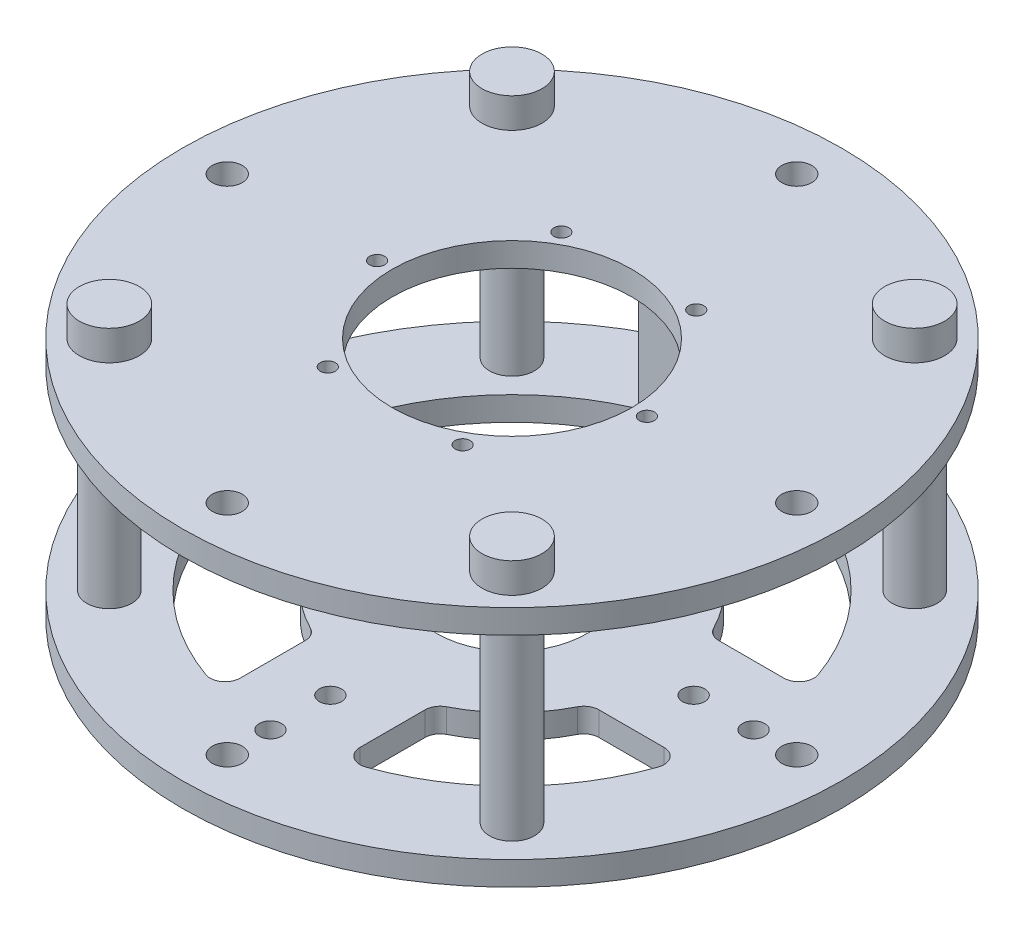
SolidWorks part; units mm, degrees
ref_plane "Front Plane" through (0, 0, 0) normal (0, 0, 1) x (1, 0, 0)
ref_plane "Top Plane" through (0, 0, 0) normal (0, 1, 0) x (1, 0, 0)
ref_plane "Right Plane" through (0, 0, 0) normal (1, 0, 0) x (0, 0, -1)
sketch "Sketch1" plane through (0, 0, 0) normal (0, 1, 0) x (1, 0, 0)
  line L0 (-25.4, 89.8026) -> (-25.4, 62.217)
  line L1 (25.4, 89.8026) -> (25.4, 62.217)
  line L2 (-25.4, 76.0098) -> (25.4, 76.0098) construction
  line L3 (0, 76.0098) -> (0, 0) construction
  line L4 (89.8026, 25.4) -> (62.217, 25.4)
  line L5 (89.8026, -25.4) -> (62.217, -25.4)
  line L6 (76.0098, 25.4) -> (76.0098, -25.4) construction
  line L7 (76.0098, 0) -> (0, 0) construction
  line L8 (25.4, -89.8026) -> (25.4, -62.217)
  line L9 (-25.4, -89.8026) -> (-25.4, -62.217)
  line L10 (25.4, -76.0098) -> (-25.4, -76.0098) construction
  line L11 (0, -76.0098) -> (0, 0) construction
  line L12 (-89.8026, -25.4) -> (-62.217, -25.4)
  line L13 (-89.8026, 25.4) -> (-62.217, 25.4)
  line L14 (-76.0098, -25.4) -> (-76.0098, 25.4) construction
  line L15 (-76.0098, 0) -> (0, 0) construction
  line L16 (0, 139.7) -> (0, 120.65) construction
  line L17 (0, 120.65) -> (0, 102.362) construction
  line L18 (0, 102.362) -> (0, 76.962) construction
  line L19 (98.7828, 98.7828) -> (85.3124, 85.3124) construction
  line L20 (139.7, 0) -> (120.65, 0) construction
  line L21 (98.7828, -98.7828) -> (85.3124, -85.3124) construction
  line L22 (0, -139.7) -> (0, -120.65) construction
  line L23 (-98.7828, -98.7828) -> (-85.3124, -85.3124) construction
  line L24 (-139.7, 0) -> (-120.65, 0) construction
  line L25 (-98.7828, 98.7828) -> (-85.3124, 85.3124) construction
  line L26 (139.7, 0) -> (120.65, 0) construction
  line L27 (120.65, 0) -> (102.362, 0) construction
  line L28 (102.362, 0) -> (76.962, 0) construction
  line L29 (0, -139.7) -> (0, -120.65) construction
  line L30 (0, -120.65) -> (0, -102.362) construction
  line L31 (0, -102.362) -> (0, -76.962) construction
  line L32 (-139.7, 0) -> (-120.65, 0) construction
  line L33 (-120.65, 0) -> (-102.362, 0) construction
  line L34 (-102.362, 0) -> (-76.962, 0) construction
  circle A0 centre (0, 0) radius 139.7
  arc A1 (-56.5609, -28.8636) -> (-28.8636, -56.5609) centre (0, 0) ccw
  arc A2 (-95.7894, -33.8667) -> (-33.8667, -95.7894) centre (0, 0) ccw
  circle A3 centre (0, 0) radius 31.75
  arc A4 (28.8636, -56.5609) -> (56.5609, -28.8636) centre (0, 0) ccw
  arc A5 (33.8667, -95.7894) -> (95.7894, -33.8667) centre (0, 0) ccw
  arc A6 (95.7894, 33.8667) -> (33.8667, 95.7894) centre (0, 0) ccw
  arc A7 (-33.8667, 95.7894) -> (-95.7894, 33.8667) centre (0, 0) ccw
  arc A8 (-28.8636, 56.5609) -> (-56.5609, 28.8636) centre (0, 0) ccw
  arc A9 (56.5609, 28.8636) -> (28.8636, 56.5609) centre (0, 0) ccw
  circle A10 centre (0, 120.65) radius 6.35
  circle A11 centre (0, 102.362) radius 4.699
  circle A12 centre (0, 76.962) radius 4.699
  circle A13 centre (85.3124, 85.3124) radius 6.35
  circle A14 centre (120.65, 0) radius 6.35
  circle A15 centre (85.3124, -85.3124) radius 6.35
  circle A16 centre (0, -120.65) radius 6.35
  circle A17 centre (-85.3124, -85.3124) radius 6.35
  circle A18 centre (-120.65, 0) radius 6.35
  circle A19 centre (-85.3124, 85.3124) radius 6.35
  circle A20 centre (120.65, 0) radius 6.35
  circle A21 centre (102.362, 0) radius 4.699
  circle A22 centre (76.962, 0) radius 4.699
  circle A23 centre (0, -120.65) radius 6.35
  circle A24 centre (0, -102.362) radius 4.699
  circle A25 centre (0, -76.962) radius 4.699
  circle A26 centre (-120.65, 0) radius 6.35
  circle A27 centre (-102.362, 0) radius 4.699
  circle A28 centre (-76.962, 0) radius 4.699
  arc A29 (-89.8026, 25.4) -> (-95.7894, 33.8667) centre (-89.8026, 31.75) cw
  arc A30 (-62.217, 25.4) -> (-56.5609, 28.8636) centre (-62.217, 31.75) ccw
  arc A31 (-25.4, 62.217) -> (-28.8636, 56.5609) centre (-31.75, 62.217) cw
  arc A32 (-25.4, 89.8026) -> (-33.8667, 95.7894) centre (-31.75, 89.8026) ccw
  arc A33 (25.4, 62.217) -> (28.8636, 56.5609) centre (31.75, 62.217) ccw
  arc A34 (25.4, 89.8026) -> (33.8667, 95.7894) centre (31.75, 89.8026) cw
  arc A35 (89.8026, 25.4) -> (95.7894, 33.8667) centre (89.8026, 31.75) ccw
  arc A36 (62.217, 25.4) -> (56.5609, 28.8636) centre (62.217, 31.75) cw
  arc A37 (89.8026, -25.4) -> (95.7894, -33.8667) centre (89.8026, -31.75) cw
  arc A38 (62.217, -25.4) -> (56.5609, -28.8636) centre (62.217, -31.75) ccw
  arc A39 (25.4, -62.217) -> (28.8636, -56.5609) centre (31.75, -62.217) cw
  arc A40 (25.4, -89.8026) -> (33.8667, -95.7894) centre (31.75, -89.8026) ccw
  arc A41 (-25.4, -89.8026) -> (-33.8667, -95.7894) centre (-31.75, -89.8026) cw
  arc A42 (-25.4, -62.217) -> (-28.8636, -56.5609) centre (-31.75, -62.217) ccw
  arc A43 (-62.217, -25.4) -> (-56.5609, -28.8636) centre (-62.217, -31.75) cw
  arc A44 (-89.8026, -25.4) -> (-95.7894, -33.8667) centre (-89.8026, -31.75) ccw
  point P37 (0, 0)
  point P63 (0, 0)
  point P86 (0, 0)
  point P90 (-25.4, 58.1987)
  point P93 (-25.4, 98.3738)
  point P96 (25.4, 58.1987)
  point P99 (25.4, 98.3738)
  dimension "D1" = 279.4
  dimension "D2" = 203.2
  dimension "D3" = 127
  dimension "D4" = 63.5
  dimension "D10" = 12.7
  dimension "D11" = 9.398
  dimension "D12" = 9.398
  dimension "D15" = 6.35
  dimension "D5" = 50.8
  dimension "D7" = 19.05
  dimension "D8" = 18.288
  dimension "D9" = 25.4
  dimension "D6" = 4
  dimension "D13" = 8
  dimension "D14" = 4
extrude "Boss-Extrude1" add sketch "Sketch1" along normal blind 10.16 contours A0 A44 L12 A43 A1 A42 L9 A41 A2 A40 L8 A39 A4 A38 L5 A37 A5 A32 L0 A31 A8 A30 L13 A29 A7 A28 A27 A25 A24 A22 A21 A19 A18 A17 A16 A15
sketch "Sketch2" plane through (0, 10.16, 0) normal (0, 1, 0) x (1, 0, 0)
  circle A0 centre (-85.3124, 85.3124) radius 9.525
  circle A1 centre (85.3124, 85.3124) radius 9.525
  circle A2 centre (85.3124, -85.3124) radius 9.525
  circle A3 centre (-85.3124, -85.3124) radius 9.525
  point P12 (0, 0)
  dimension "D1" = 19.05
  dimension "D2" = 4
extrude "Boss-Extrude2" add sketch "Sketch2" along normal blind 82.296
sketch "Sketch3" plane through (0, 92.456, 0) normal (0, 1, 0) x (1, 0, 0)
  circle A0 centre (0, 0) radius 139.7
  circle A1 centre (0, 0) radius 139.7 construction
  circle A2 centre (0, 0) radius 50.8
  circle A3 centre (0, 120.65) radius 6.35
  circle A4 centre (85.3124, 85.3124) radius 6.35
  circle A5 centre (120.65, 0) radius 6.35
  circle A6 centre (85.3124, -85.3124) radius 6.35
  circle A7 centre (0, -120.65) radius 6.35
  circle A8 centre (-85.3124, -85.3124) radius 6.35
  circle A9 centre (-120.65, 0) radius 6.35
  circle A10 centre (-85.3124, 85.3124) radius 6.35
  circle A11 centre (-57.15, 0) radius 3.175
  circle A12 centre (-28.575, 49.4934) radius 3.175
  circle A13 centre (28.575, 49.4934) radius 3.175
  circle A14 centre (57.15, 0) radius 3.175
  circle A15 centre (28.575, -49.4934) radius 3.175
  circle A16 centre (-28.575, -49.4934) radius 3.175
  point P25 (0, 0)
  point P39 (0, 0)
  dimension "D1" = 101.6
  dimension "D3" = 6.35
  dimension "D4" = 63.5
  dimension "D2" = 8
  dimension "D5" = 6
extrude "Boss-Extrude3" add sketch "Sketch3" along normal blind 10.16
sketch "Sketch4" plane through (0, 102.616, 0) normal (0, 1, 0) x (1, 0, 0)
  circle A0 centre (-85.3124, 85.3124) radius 12.7
  circle A1 centre (85.3124, 85.3124) radius 12.7
  circle A2 centre (85.3124, -85.3124) radius 12.7
  circle A3 centre (-85.3124, -85.3124) radius 12.7
  point P12 (0, 0)
  dimension "D1" = 25.4
  dimension "D2" = 4
extrude "Boss-Extrude4" add sketch "Sketch4" along normal blind 12.7
sketch "Sketch6" plane through (0, 10.16, 0) normal (0, 1, 0) x (1, 0, 0)
  line L0 (0, 0) -> (0, 63.5) construction
  line L1 (9.906, 63.5) -> (-9.906, 63.5)
  line L2 (9.906, 63.5) -> (9.906, 114.3)
  line L3 (9.906, 114.3) -> (-9.906, 114.3)
  line L4 (-9.906, 63.5) -> (-9.906, 114.3)
  line L5 (9.906, 63.5) -> (-9.906, 114.3) construction
  line L6 (9.906, 114.3) -> (-9.906, 63.5) construction
  line L7 (0, 114.3) -> (0, 139.7) construction
  circle A2 centre (0, 0) radius 139.7 construction
  point P0 (0, 88.9)
  dimension "D1" = 19.812
  dimension "D2" = 50.8
  dimension "D3" = 25.4
extrude "Boss-Extrude5" add sketch "Sketch6" along normal blind 76.2
sketch "Sketch7" plane through (9.906, 0, 0) normal (1, 0, 0) x (0, 0, -1)
  line L0 (114.3, 86.36) -> (114.3, 10.16) construction
  line L2 (66.8157, 52.373) -> (82.7921, 52.373)
  line L3 (66.8157, 52.373) -> (66.8157, 49.3372)
  line L4 (66.8157, 49.3372) -> (82.7921, 49.3372)
  line L6 (66.8157, 52.373) -> (82.6999, 50.8551) construction
  line L7 (66.8157, 49.3372) -> (82.6999, 50.8551) construction
  arc A0 (82.7921, 49.3372) -> (82.7921, 52.373) centre (95.25, 50.8551) ccw
  point P2 (82.6999, 50.8551)
  dimension "D1" = 3.0358
  dimension "D2" = 19.05
